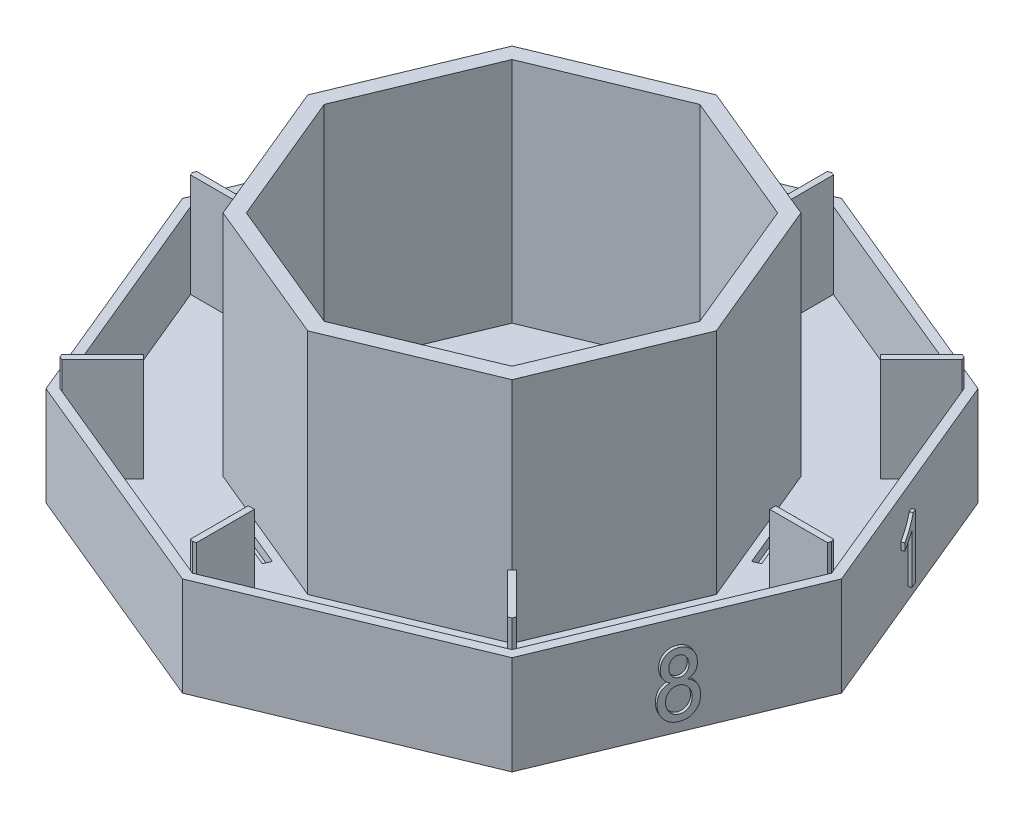
SolidWorks part; units mm, degrees
ref_plane "Front Plane" through (0, 0, 0) normal (0, 0, 1) x (1, 0, 0)
ref_plane "Top Plane" through (0, 0, 0) normal (0, 1, 0) x (1, 0, 0)
ref_plane "Right Plane" through (0, 0, 0) normal (1, 0, 0) x (0, 0, -1)
sketch "Croquis1" plane through (0, 0, 0) normal (0, 1, 0) x (1, 0, 0)
  line L1 (76.5367, 76.5367) -> (0, 108.2392)
  line L2 (0, 108.2392) -> (-76.5367, 76.5367)
  line L3 (-76.5367, 76.5367) -> (-108.2392, 0)
  line L4 (-108.2392, 0) -> (-76.5367, -76.5367)
  line L5 (-76.5367, -76.5367) -> (0, -108.2392)
  line L6 (0, -108.2392) -> (76.5367, -76.5367)
  line L7 (76.5367, -76.5367) -> (108.2392, 0)
  line L8 (108.2392, 0) -> (76.5367, 76.5367)
  circle A1 centre (0, 0) radius 100 construction
  dimension "D2" = 100
extrude "Saliente-Extruir1" add sketch "Croquis1" along normal blind 7.5 contours L7 L8 L1 L2 L3 L4 L5 L6
sketch "Croquis2" plane through (0, 7.5, 0) normal (0, 1, 0) x (1, 0, 0)
  circle A1 centre (0, 0) radius 4.25
  circle A2 centre (0, 0) radius 10 construction
  circle A13 centre (0, 10) radius 1.5
  circle A14 centre (10, 0) radius 1.5
  circle A15 centre (0, -10) radius 1.5
  circle A16 centre (-10, 0) radius 1.5
  point P15 (0, 0)
  point P22 (0, 0)
  dimension "D1" = 8.5
  dimension "D2" = 20
  dimension "D3" = 3
  dimension "D6" = 20
  dimension "D5" = 10
  dimension "D4" = 4
sketch "Croquis3" plane through (0, 7.5, 0) normal (0, 1, 0) x (1, 0, 0)
  line L1 (0, 67.1083) -> (-47.4527, 47.4527)
  line L2 (-47.4527, 47.4527) -> (-67.1083, 0)
  line L3 (-67.1083, 0) -> (-47.4527, -47.4527)
  line L4 (-47.4527, -47.4527) -> (0, -67.1083)
  line L5 (0, -67.1083) -> (47.4527, -47.4527)
  line L6 (47.4527, -47.4527) -> (67.1083, 0)
  line L7 (67.1083, 0) -> (47.4527, 47.4527)
  line L8 (47.4527, 47.4527) -> (0, 67.1083)
  line L9 (-76.5367, 76.5367) -> (-108.2392, 0) construction
  line L11 (0, 61.6964) -> (-43.6259, 43.6259)
  line L12 (-43.6259, 43.6259) -> (-61.6964, 0)
  line L13 (-61.6964, 0) -> (-43.6259, -43.6259)
  line L14 (-43.6259, -43.6259) -> (0, -61.6964)
  line L15 (0, -61.6964) -> (43.6259, -43.6259)
  line L16 (43.6259, -43.6259) -> (61.6964, 0)
  line L17 (61.6964, 0) -> (43.6259, 43.6259)
  line L18 (43.6259, 43.6259) -> (0, 61.6964)
  circle A2 centre (0, 0) radius 62 construction
  circle A3 centre (0, 0) radius 57 construction
  dimension "D1" = 38
  dimension "D2" = 5
extrude "Saliente-Extruir2" add sketch "Croquis3" along normal blind 75
sketch "Croquis4" plane through (0, 7.5, 0) normal (0, 1, 0) x (1, 0, 0)
  line L1 (0, 108.2392) -> (-76.5367, 76.5367)
  line L2 (-76.5367, 76.5367) -> (-108.2392, 0)
  line L3 (-108.2392, 0) -> (-76.5367, -76.5367)
  line L4 (-76.5367, -76.5367) -> (0, -108.2392)
  line L5 (0, -108.2392) -> (76.5367, -76.5367)
  line L6 (76.5367, -76.5367) -> (108.2392, 0)
  line L7 (108.2392, 0) -> (76.5367, 76.5367)
  line L8 (76.5367, 76.5367) -> (0, 108.2392)
  line L9 (0, 104.992) -> (-74.2406, 74.2406)
  line L10 (-74.2406, 74.2406) -> (-104.992, 0)
  line L11 (-104.992, 0) -> (-74.2406, -74.2406)
  line L12 (-74.2406, -74.2406) -> (0, -104.992)
  line L13 (0, -104.992) -> (74.2406, -74.2406)
  line L14 (74.2406, -74.2406) -> (104.992, 0)
  line L15 (104.992, 0) -> (74.2406, 74.2406)
  line L16 (74.2406, 74.2406) -> (0, 104.992)
  circle A2 centre (0, 0) radius 100 construction
  circle A3 centre (0, 0) radius 97 construction
  dimension "D3" = 97
  dimension "D4" = 100
extrude "Saliente-Extruir3" add sketch "Croquis4" along normal blind 25
sketch "Croquis5" plane through (0, 7.5, 0) normal (0, 1, 0) x (1, 0, 0)
  line L0 (-74.2406, -74.2406) -> (-47.4527, -47.4527) construction
  line L1 (-73.2406, -74.6548) -> (-46.4527, -47.867)
  line L2 (-74.2406, -74.2406) -> (0, -104.992) construction
  line L3 (-47.4527, -47.4527) -> (0, -67.1083) construction
  line L4 (-74.6548, -73.2406) -> (-47.867, -46.4527)
  line L5 (-104.992, 0) -> (-74.2406, -74.2406) construction
  line L6 (-67.1083, 0) -> (-47.4527, -47.4527) construction
  line L7 (-73.2406, -74.6548) -> (-74.2406, -74.2406)
  line L8 (-74.2406, -74.2406) -> (-74.6548, -73.2406)
  line L9 (-46.4527, -47.867) -> (-47.4527, -47.4527)
  line L10 (-47.4527, -47.4527) -> (-47.867, -46.4527)
  line L11 (-67.1083, 0) -> (-66.6941, 1)
  line L12 (-104.5778, 1) -> (-66.6941, 1)
  line L13 (-104.992, 0) -> (-104.5778, 1)
  line L14 (-104.5778, -1) -> (-104.992, 0)
  line L15 (-104.5778, -1) -> (-66.6941, -1)
  line L16 (-66.6941, -1) -> (-67.1083, 0)
  line L17 (-47.4527, 47.4527) -> (-46.4527, 47.867)
  line L18 (-73.2406, 74.6548) -> (-46.4527, 47.867)
  line L19 (-74.2406, 74.2406) -> (-73.2406, 74.6548)
  line L20 (-74.6548, 73.2406) -> (-74.2406, 74.2406)
  line L21 (-74.6548, 73.2406) -> (-47.867, 46.4527)
  line L22 (-47.867, 46.4527) -> (-47.4527, 47.4527)
  line L23 (0, 67.1083) -> (1, 66.6941)
  line L24 (1, 104.5778) -> (1, 66.6941)
  line L25 (0, 104.992) -> (1, 104.5778)
  line L26 (-1, 104.5778) -> (0, 104.992)
  line L27 (-1, 104.5778) -> (-1, 66.6941)
  line L28 (-1, 66.6941) -> (0, 67.1083)
  line L29 (47.4527, 47.4527) -> (47.867, 46.4527)
  line L30 (74.6548, 73.2406) -> (47.867, 46.4527)
  line L31 (74.2406, 74.2406) -> (74.6548, 73.2406)
  line L32 (73.2406, 74.6548) -> (74.2406, 74.2406)
  line L33 (73.2406, 74.6548) -> (46.4527, 47.867)
  line L34 (46.4527, 47.867) -> (47.4527, 47.4527)
  line L35 (67.1083, 0) -> (66.6941, -1)
  line L36 (104.5778, -1) -> (66.6941, -1)
  line L37 (104.992, 0) -> (104.5778, -1)
  line L38 (104.5778, 1) -> (104.992, 0)
  line L39 (104.5778, 1) -> (66.6941, 1)
  line L40 (66.6941, 1) -> (67.1083, 0)
  line L41 (47.4527, -47.4527) -> (46.4527, -47.867)
  line L42 (73.2406, -74.6548) -> (46.4527, -47.867)
  line L43 (74.2406, -74.2406) -> (73.2406, -74.6548)
  line L44 (74.6548, -73.2406) -> (74.2406, -74.2406)
  line L45 (74.6548, -73.2406) -> (47.867, -46.4527)
  line L46 (47.867, -46.4527) -> (47.4527, -47.4527)
  line L47 (0, -67.1083) -> (-1, -66.6941)
  line L48 (-1, -104.5778) -> (-1, -66.6941)
  line L49 (0, -104.992) -> (-1, -104.5778)
  line L50 (1, -104.5778) -> (0, -104.992)
  line L51 (1, -104.5778) -> (1, -66.6941)
  line L52 (1, -66.6941) -> (0, -67.1083)
  line L53 (0, -104.992) -> (74.2406, -74.2406) construction
  line L54 (85.636, -1) -> (85.636, 1)
  line L55 (61.2609, 59.8467) -> (59.8467, 61.2609)
  line L56 (1, 85.636) -> (-1, 85.636)
  line L57 (-59.8467, 61.2609) -> (-61.2609, 59.8467)
  line L58 (-85.636, 1) -> (-85.636, -1)
  line L59 (-61.2609, -59.8467) -> (-59.8467, -61.2609)
  line L60 (1, -85.636) -> (-1, -85.636)
  line L61 (61.2609, -59.8467) -> (59.8467, -61.2609)
  point P61 (0, 0)
  line M10 (74.2406, 74.2406) -> (0, 104.992)
  line M11 (0, 104.992) -> (-74.2406, 74.2406)
  line M12 (-74.2406, 74.2406) -> (-104.992, 0)
  line M13 (-104.992, 0) -> (-74.2406, -74.2406)
  line M14 (-74.2406, -74.2406) -> (0, -104.992)
  line M15 (0, -104.992) -> (74.2406, -74.2406)
  line M16 (74.2406, -74.2406) -> (104.992, 0)
  line M17 (104.992, 0) -> (74.2406, 74.2406)
  dimension "D1" = 1
  dimension "D2" = 1
  dimension "D4" = 67.1083
  dimension "D5" = 35
  dimension "D3" = 8
extrude "Saliente-Extruir4" add sketch "Croquis5" along normal blind 34 contours L54 L36 L39 M16 M17 | L45 L61 L42 M15 M16 | L51 L60 L48 M14 M15 | L0 L59 L4 M13 | L0 L1 L59 M14 | L58 L12 L15 M12 M13 | L57 L18 L21 M11 M12 | L56 L24 L27 M10 M11 | L55 L30 L33 M17 M10
sketch "Croquis7" plane through (0, 0, 0) normal (0, -1, 0) x (1, 0, 0)
  line L0 (-92.388, -38.2683) -> (0, 0) construction
  line L1 (-76.5367, -76.5367) -> (-108.2392, 0) construction
  line L2 (-38.2683, -92.388) -> (0, 0) construction
  line L3 (0, -108.2392) -> (-76.5367, -76.5367) construction
  line L4 (38.2683, -92.388) -> (0, 0) construction
  line L5 (76.5367, -76.5367) -> (0, -108.2392) construction
  line L6 (92.388, -38.2683) -> (0, 0) construction
  line L7 (108.2392, 0) -> (76.5367, -76.5367) construction
  line L8 (92.388, 38.2683) -> (0, 0) construction
  line L9 (76.5367, 76.5367) -> (108.2392, 0) construction
  line L10 (0, 0) -> (-38.2683, 92.388) construction
  line L11 (-76.5367, 76.5367) -> (0, 108.2392) construction
  line L12 (38.2683, 92.388) -> (0, 0) construction
  line L13 (0, 108.2392) -> (76.5367, 76.5367) construction
  line L14 (0, 0) -> (-92.388, 38.2683) construction
  line L15 (-108.2392, 0) -> (-76.5367, 76.5367) construction
  circle A0 centre (0, 0) radius 90 construction
  circle A1 centre (-83.1492, 34.4415) radius 3.2
  circle A2 centre (-34.4415, 83.1492) radius 3.2
  circle A3 centre (34.4415, 83.1492) radius 3.2
  circle A4 centre (83.1492, 34.4415) radius 3.2
  circle A5 centre (83.1492, -34.4415) radius 3.2
  circle A6 centre (34.4415, -83.1492) radius 3.2
  circle A7 centre (-34.4415, -83.1492) radius 3.2
  circle A8 centre (-83.1492, -34.4415) radius 3.2
  circle A12 centre (-46.194, 19.1342) radius 3.2
  point P45 (0, 0)
  dimension "D1" = 180
  dimension "D2" = 6.4
  dimension "D4" = 83.1492
  dimension "D7" = 6.4
  dimension "D5" = 48.7076
  dimension "D3" = 8
extrude "Cortar-Extruir2" cut sketch "Croquis7" against normal blind 5
extrude "Cortar-Extruir3" cut sketch "Croquis2" against normal blind 7.5
sketch "Croquis8" plane through (0, 7.5, 0) normal (0, 1, 0) x (1, 0, 0)
  line L1 (34.1528, 55.6677) -> (35.1096, 57.9774)
  line L2 (35.1096, 57.9774) -> (16.17, 65.8224)
  line L3 (16.17, 65.8224) -> (15.2133, 63.5127)
  line L5 (47.4527, 47.4527) -> (0, 67.1083) construction
  line L6 (23.7264, 57.2805) -> (26.6037, 64.2271) construction
  line L7 (34.1528, 55.6677) -> (15.2133, 63.5127)
  point P7 (15.6917, 64.6676)
  dimension "D1" = 2.5
  dimension "D2" = 2.5
  dimension "D3" = 20.5
  dimension "D4" = 10.25
  dimension "D5" = 2.5
extrude "Cortar-Extruir4" cut sketch "Croquis8" against normal blind 3
pattern_circular "MatrizC1" count 8 over 360 about axis through (0, 0, 0) along (0, 1, 0) of "Cortar-Extruir4"
sketch "Croquis10" plane through (92.388, 0, -38.2683) normal (0.9239, 0, -0.3827) x (-0.3827, 0, -0.9239)
  line L0 (-7.7914, 4) -> (22.7862, 4) construction
  line L1 (0, 0) -> (0, 12.282) construction
  line L2 (-41.4214, 0) -> (41.4214, 0) construction
  text T0 "1" font "Arial Narrow" height in points 80
  dimension "D1" = 4
extrude "Saliente-Extruir6" add sketch "Croquis10" along normal blind 1
sketch "Croquis11" plane through (92.388, 0, 38.2683) normal (0.9239, 0, 0.3827) x (0.3827, 0, -0.9239)
  line L0 (-6.4233, 4) -> (7.1912, 4) construction
  line L1 (0, 0) -> (0, 22.5305) construction
  line L3 (-41.4214, 0) -> (41.4214, 0) construction
  text T0 "8" font "Arial Narrow" height in points 80
  dimension "D1" = 4
extrude "Saliente-Extruir7" add sketch "Croquis11" along normal blind 1
